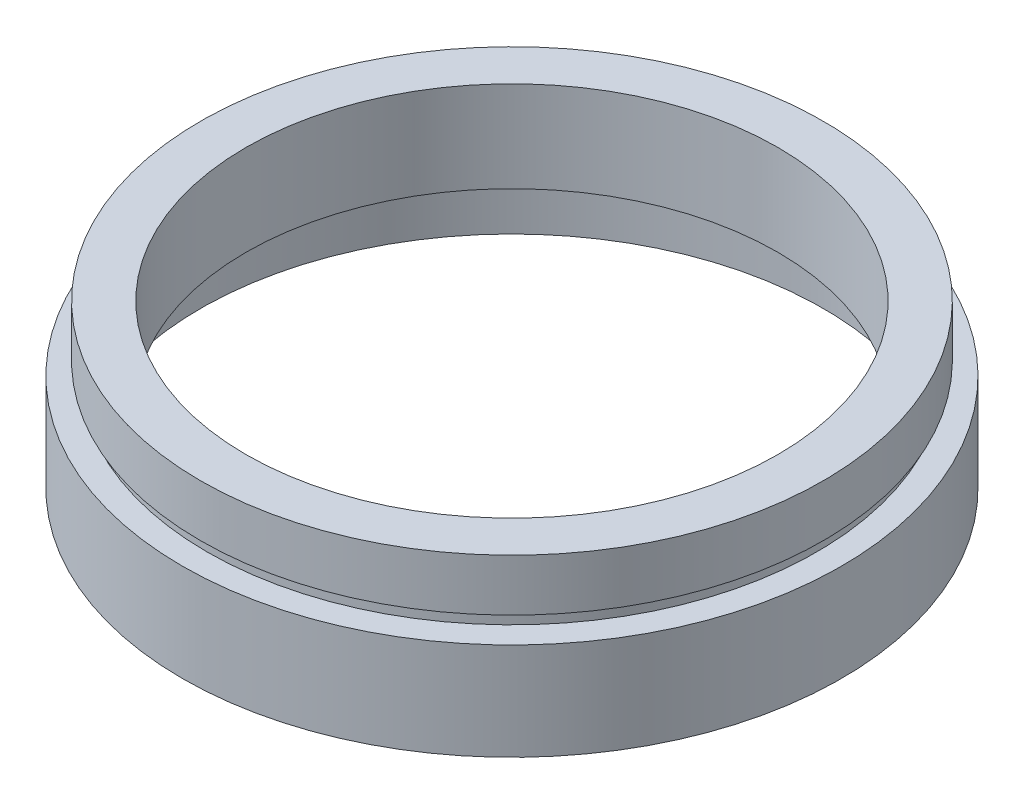
SolidWorks part; units mm, degrees
ref_plane "前视基准面" through (0, 0, 0) normal (0, 0, 1) x (1, 0, 0)
ref_plane "上视基准面" through (0, 0, 0) normal (0, 1, 0) x (1, 0, 0)
ref_plane "右视基准面" through (0, 0, 0) normal (1, 0, 0) x (0, 0, -1)
sketch "草图1" plane through (0, 0, 0) normal (0, 0, 1) x (1, 0, 0)
  line L0 (0, 161.3762) -> (0, 0) construction
  line L1 (141.7365, 0) -> (-131.7984, 0) construction
  line L2 (20.5, 12.5) -> (24, 12.5)
  line L3 (24, 12.5) -> (24, 8.5)
  line L4 (24, 8.5) -> (23.5, 8.5)
  line L5 (23.5, 8.5) -> (23.5, 7.5)
  line L6 (23.5, 7.5) -> (25.4, 7.5)
  line L7 (25.4, 7.5) -> (25.4, 0)
  line L8 (25.4, 0) -> (24, 0)
  line L9 (24, 0) -> (24, 4.5)
  line L10 (24, 4.5) -> (24.1, 4.5)
  line L11 (24.1, 4.5) -> (24.1, 5.5)
  line L12 (24.1, 5.5) -> (20.5, 5.5)
  line L13 (20.5, 5.5) -> (20.5, 12.5)
  dimension "D1" = 20.5
  dimension "D2" = 24
  dimension "D3" = 1
  dimension "D4" = 1
  dimension "D5" = 23.5
  dimension "D6" = 24.1
  dimension "D7" = 24
  dimension "D8" = 5
  dimension "D9" = 7
  dimension "D10" = 7.5
  dimension "D11" = 25.4
revolve "旋转1" add sketch "草图1" angle 360 about L0
cosmetic thread "装饰螺纹线1" parameters "D2"=48.1
cosmetic thread "装饰螺纹线2" parameters "D2"=42
cosmetic thread "装饰螺纹线3" parameters "D2"=47
